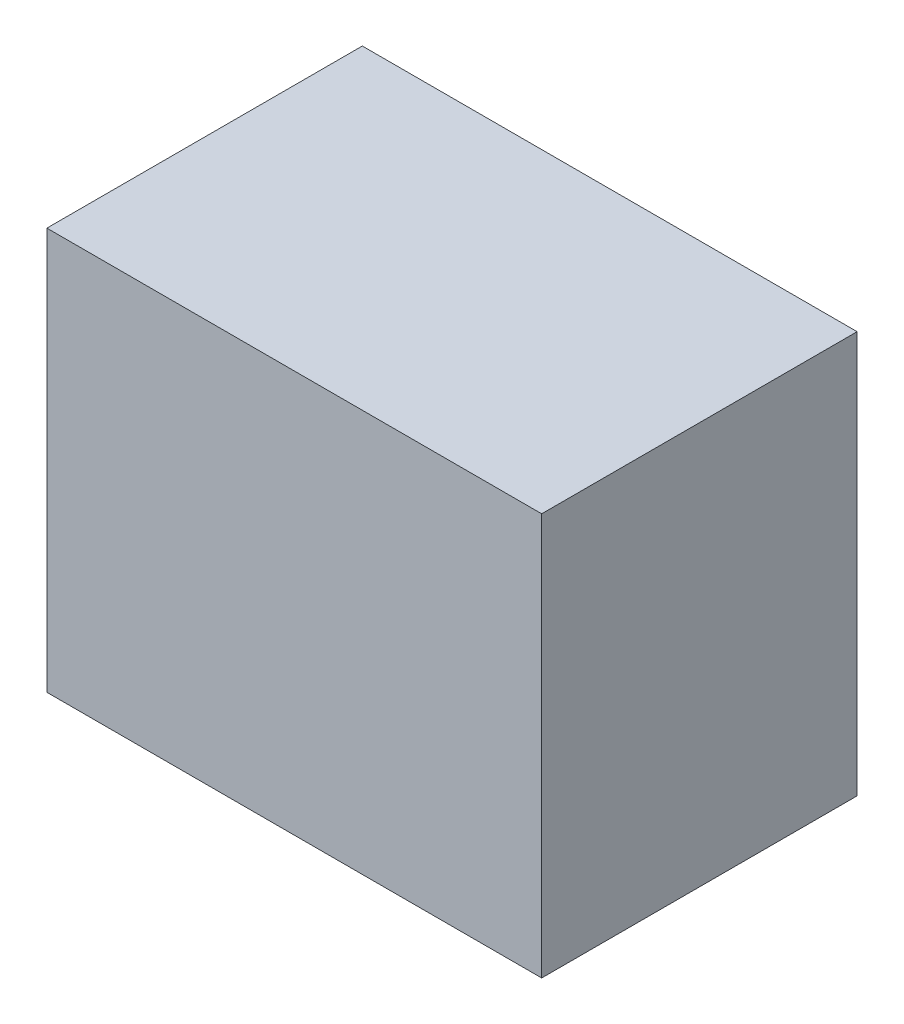
SolidWorks part; units mm, degrees
ref_plane "Front Plane" through (0, 0, 0) normal (0, 0, 1) x (1, 0, 0)
ref_plane "Top Plane" through (0, 0, 0) normal (0, 1, 0) x (1, 0, 0)
ref_plane "Right Plane" through (0, 0, 0) normal (1, 0, 0) x (0, 0, -1)
sketch "Sketch1" plane through (0, 0, 0) normal (0, 0, 1) x (1, 0, 0)
  line L1 (80, -65) -> (-80, -65)
  line L2 (80, -65) -> (80, 65)
  line L3 (80, 65) -> (-80, 65)
  line L4 (-80, -65) -> (-80, 65)
  line L5 (80, -65) -> (-80, 65) construction
  line L6 (80, 65) -> (-80, -65) construction
  point P0 (0, 0)
  dimension "D1" = 130
  dimension "D2" = 160
extrude "Boss-Extrude1" add sketch "Sketch1" along normal blind 102
